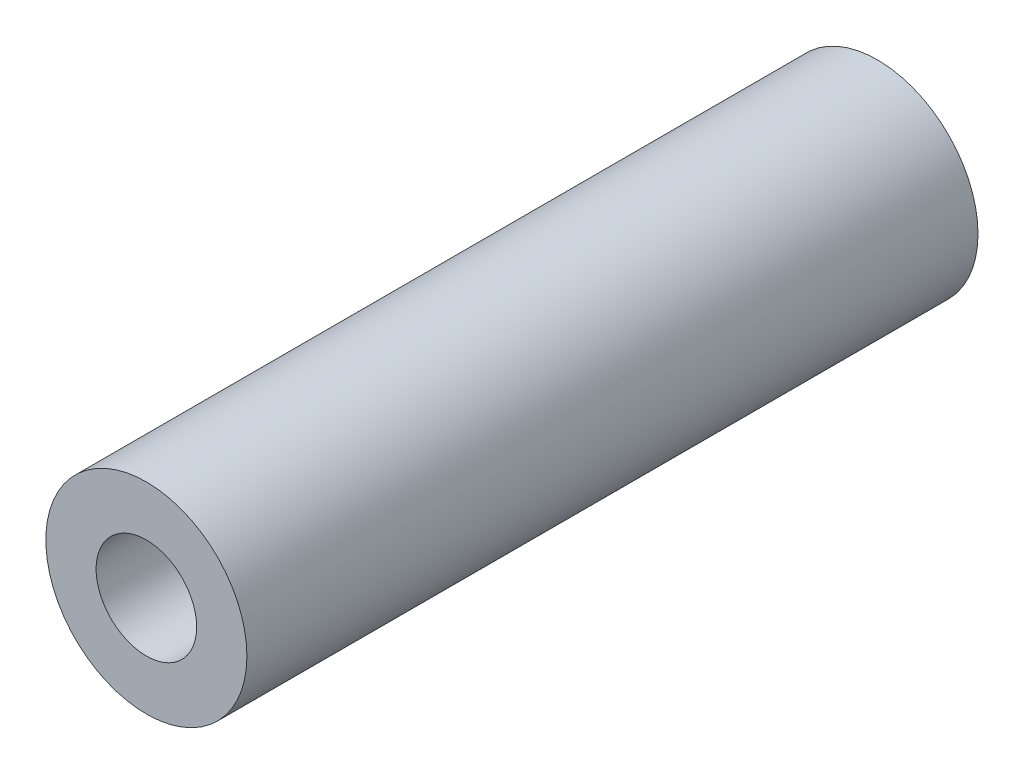
SolidWorks part; units mm, degrees
ref_plane "Front Plane" through (0, 0, 0) normal (0, 0, 1) x (1, 0, 0)
ref_plane "Top Plane" through (0, 0, 0) normal (0, 1, 0) x (1, 0, 0)
ref_plane "Right Plane" through (0, 0, 0) normal (1, 0, 0) x (0, 0, -1)
sketch "Sketch1" plane through (0, 0, 0) normal (0, 0, 1) x (1, 0, 0)
  circle A0 centre (0, 0) radius 5.5
  circle A1 centre (0, 0) radius 11
  dimension "D1" = 11
  dimension "D2" = 22
extrude "Boss-Extrude1" add sketch "Sketch1" along normal mid plane 80
